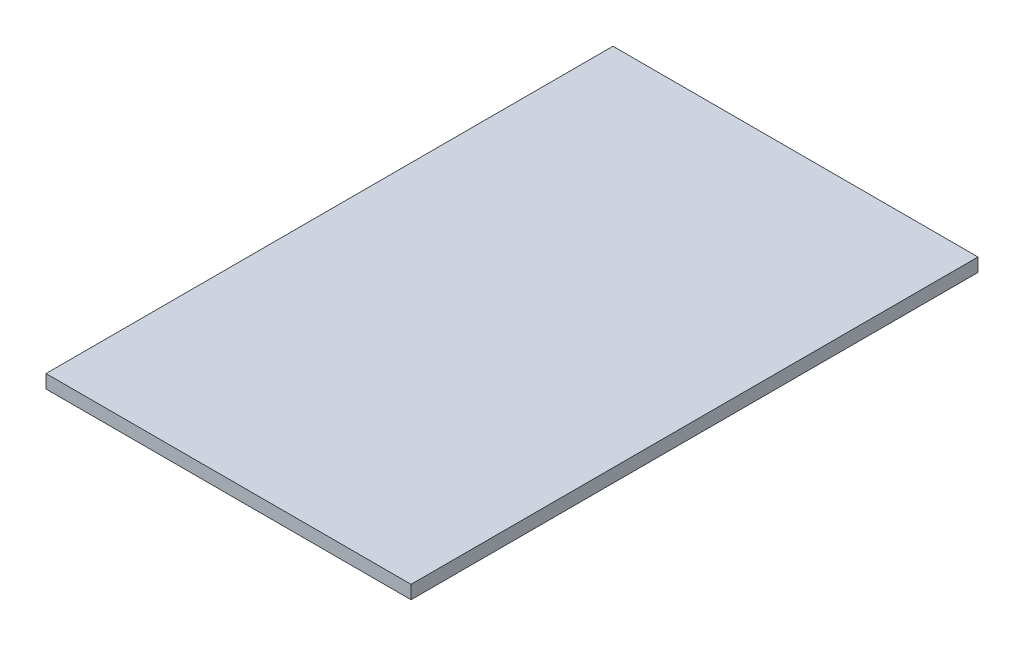
SolidWorks part; units mm, degrees
ref_plane "Спереди" through (0, 0, 0) normal (0, 0, 1) x (1, 0, 0)
ref_plane "Сверху" through (0, 0, 0) normal (0, 1, 0) x (1, 0, 0)
ref_plane "Справа" through (0, 0, 0) normal (1, 0, 0) x (0, 0, -1)
sketch "Эскиз1" plane through (0, 0, 0) normal (0, 1, 0) x (1, 0, 0)
  line L1 (245, -380.5) -> (-245, -380.5)
  line L2 (245, -380.5) -> (245, 380.5)
  line L3 (245, 380.5) -> (-245, 380.5)
  line L4 (-245, -380.5) -> (-245, 380.5)
  line L5 (245, -380.5) -> (-245, 380.5) construction
  line L6 (245, 380.5) -> (-245, -380.5) construction
  point P0 (0, 0)
  dimension "D1" = 490
  dimension "D2" = 761
extrude "Бобышка-Вытянуть1" add sketch "Эскиз1" along normal blind 18
